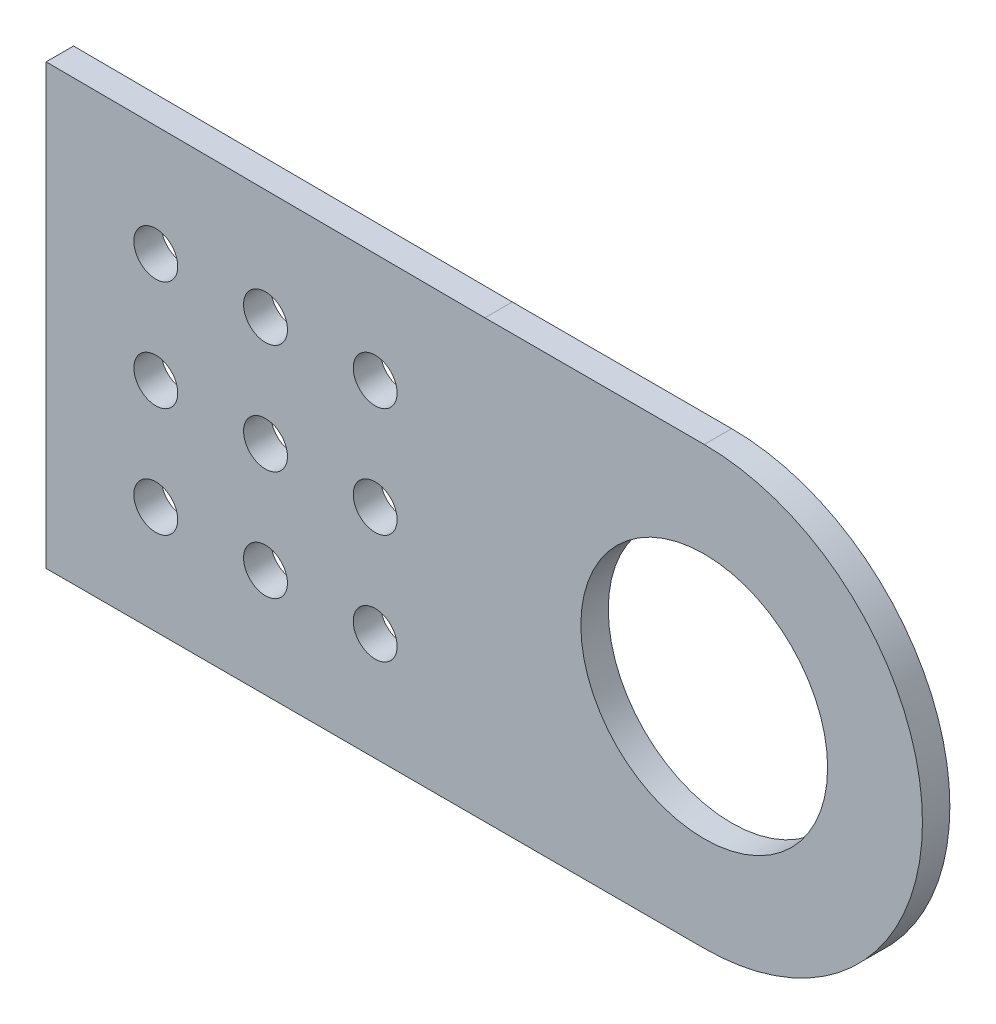
SolidWorks part; units mm, degrees
ref_plane "Front Plane" through (0, 0, 0) normal (0, 0, 1) x (1, 0, 0)
ref_plane "Top Plane" through (0, 0, 0) normal (0, 1, 0) x (1, 0, 0)
ref_plane "Right Plane" through (0, 0, 0) normal (1, 0, 0) x (0, 0, -1)
sketch "Sketch1" plane through (0, 0, 0) normal (0, 0, 1) x (1, 0, 0)
  line L0 (0, 0) -> (0, 50.8)
  line L6 (0, 50.8) -> (50.8, 50.5344)
  line L7 (50.8, 50.5344) -> (76.2, 50.5344)
  line L12 (0, 0) -> (76.2, 0)
  circle A1 centre (12.7, 37.9006) radius 2.54
  circle A2 centre (25.4, 37.9006) radius 2.54
  circle A3 centre (38.1, 37.9006) radius 2.54
  circle A4 centre (25.4, 25.2006) radius 2.54
  circle A5 centre (38.1, 25.2006) radius 2.54
  circle A6 centre (25.4, 12.5006) radius 2.54
  circle A7 centre (38.1, 12.5006) radius 2.54
  circle A8 centre (12.7, 25.2006) radius 2.54
  circle A9 centre (12.7, 12.5006) radius 2.54
  circle A11 centre (76.2, -0.1657) radius 15.5575 construction
  circle A12 centre (76.2, -0.1657) radius 15.5575 construction
  arc A13 (76.2, 0) -> (76.2, 50.5344) centre (76.2, 25.2672) ccw
  circle A14 centre (76.2, 25.2672) radius 14.2875
  point P8 (0, 0)
  point P10 (0, 0)
  point P29 (0, 0)
  point P30 (0, 0)
  point P31 (0, 0)
  point P35 (0, 0)
  point P36 (0, 0)
  point P37 (25.4, 13.1244)
  point P38 (25.2187, 12.5006)
  point P39 (0, 0)
  dimension "D3" = 5.08
  dimension "D5" = 28.575
  dimension "D1" = 50.8
  dimension "D2" = 12.7
  dimension "D4" = 12.7
  dimension "D8" = 12.7
  dimension "D9" = 12.7
  dimension "D6" = 12.7
  dimension "D7" = 12.7
extrude "Boss-Extrude1" add sketch "Sketch1" along normal blind 3.175
